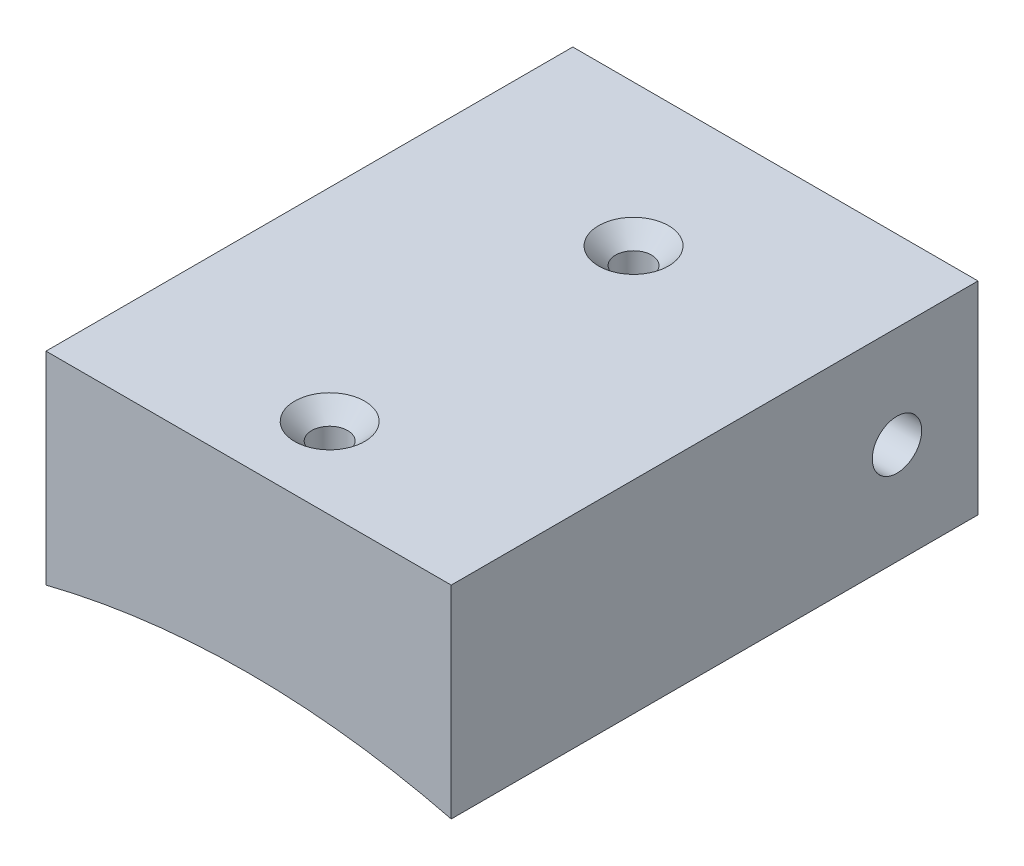
SolidWorks part; units mm, degrees
material "6061-T6 (SS)"
ref_plane "Front Plane" through (0, 0, 0) normal (0, 0, 1) x (1, 0, 0)
ref_plane "Top Plane" through (0, 0, 0) normal (0, 1, 0) x (1, 0, 0)
ref_plane "Right Plane" through (0, 0, 0) normal (1, 0, 0) x (0, 0, -1)
sketch "Sketch1" plane through (0, 0, 0) normal (0, 0, 1) x (1, 0, 0)
  line L0 (0, 0) -> (0, -17.6767) construction
  line L1 (0, 41.016) -> (-33.3169, 41.016) construction
  line L2 (-10, 39.7783) -> (-10, 49.7783)
  line L3 (-10, 49.7783) -> (10, 49.7783)
  line L4 (10, 39.7783) -> (10, 49.7783)
  line L5 (-20.2233, 23.2958) -> (10, 49.7783) construction
  line L6 (-10, 49.7783) -> (17.1226, 26.0126) construction
  arc A0 (10, 39.7783) -> (-10, 39.7783) centre (0, 0) ccw
  point P1 (0, 49.7783)
  point P3 (0, 41.016)
  dimension "D1" = 41.016
  dimension "D2" = 20
  dimension "D3" = 10
extrude "Boss-Extrude1" add sketch "Sketch1" along normal mid plane 23
hole_wizard "#2-56 Tapped Hole3" positions "Sketch9" profile "Sketch8" tap size "#2-56" standard "ANSI Inch" end condition through all
sketch "Sketch9" plane through (0, 49.7783, 0) normal (0, 1, 0) x (1, 0, 0)
  line L0 (0, 0) -> (0, -2.7876) construction
  line L1 (10, -11.5) -> (-10, -11.5) construction
  point P0 (0, -7.5)
  point P7 (0, 7.5)
  dimension "D1" = 4
  dimension "D2" = 15
sketch "Sketch8" plane through (0, 49.7783, 7.5) normal (1, 0, 0) x (0, 0, 1)
  line L0 (0, 0) -> (0, 10)
  line L1 (0, 10) -> (0.889, 10)
  line L2 (0.889, 10) -> (0.889, 0.8382)
  line L3 (0.889, 0.8382) -> (1.7272, 0)
  line L5 (1.7272, 0) -> (0, 0)
  line L6 (-0.889, 0.8382) -> (-1.7272, 0) construction
  line L11 (0, -6.35) -> (0, 107.95) construction
  dimension "Thru Tap Drill Dia." = 1.778
  dimension "Thru Tap Drill Depth" = 10
  dimension "Near C'Sink Dia." = 3.4544
  dimension "Near C'Sink Angle" = 90
cosmetic thread "Hole Thread5" parameters "D2"=2.1844
cosmetic thread "Hole Thread7" parameters "D2"=2.1844
sketch "Sketch5" plane through (0, 0, -11.5) normal (0, 0, -1) x (-1, 0, 0)
  line L3 (10, 49.7783) -> (-10, 49.7783)
  line L4 (10, 39.7783) -> (10, 49.7783)
  line L5 (10, 49.7783) -> (-10, 49.7783)
  line L6 (-10, 49.7783) -> (-10, 39.7783)
  line L7 (10, 39.7783) -> (10, 49.7783)
  line L9 (-10, 49.7783) -> (-10, 39.7783)
  arc A1 (10, 39.7783) -> (-10, 39.7783) centre (0, 0) ccw
  arc A2 (10, 39.7783) -> (-10, 39.7783) centre (0, 0) ccw
  dimension "D1" = 0
extrude "Boss-Extrude2" add sketch "Sketch5" along normal blind 3
hole_wizard "#2 Clearance Hole1" positions "Sketch13" profile "Sketch12" hole size "#2" standard "ANSI Inch" end condition through all
sketch "Sketch13" plane through (-10, 0, 0) normal (-1, 0, 0) x (0, 0, 1)
  line L0 (-14.5, 44.7783) -> (-24.3841, 44.7783) construction
  line L1 (-14.5, 39.7783) -> (-14.5, 49.7783) construction
  line L3 (11.5, 49.7783) -> (11.5, 39.7783) construction
  point P8 (-10.5, 44.7783)
  dimension "D1" = 22
sketch "Sketch12" plane through (-10, 44.7783, -10.5) normal (0, 1, 0) x (0, 0, 1)
  line L0 (0, 0) -> (0, 20)
  line L1 (0, 20) -> (1.2192, 20)
  line L2 (1.2192, 20) -> (1.2192, 0)
  line L5 (1.2192, 0) -> (0, 0)
  line L11 (0, -6.35) -> (0, 107.95) construction
  dimension "Thru Hole Dia." = 2.4384
  dimension "Thru Hole Depth" = 20
